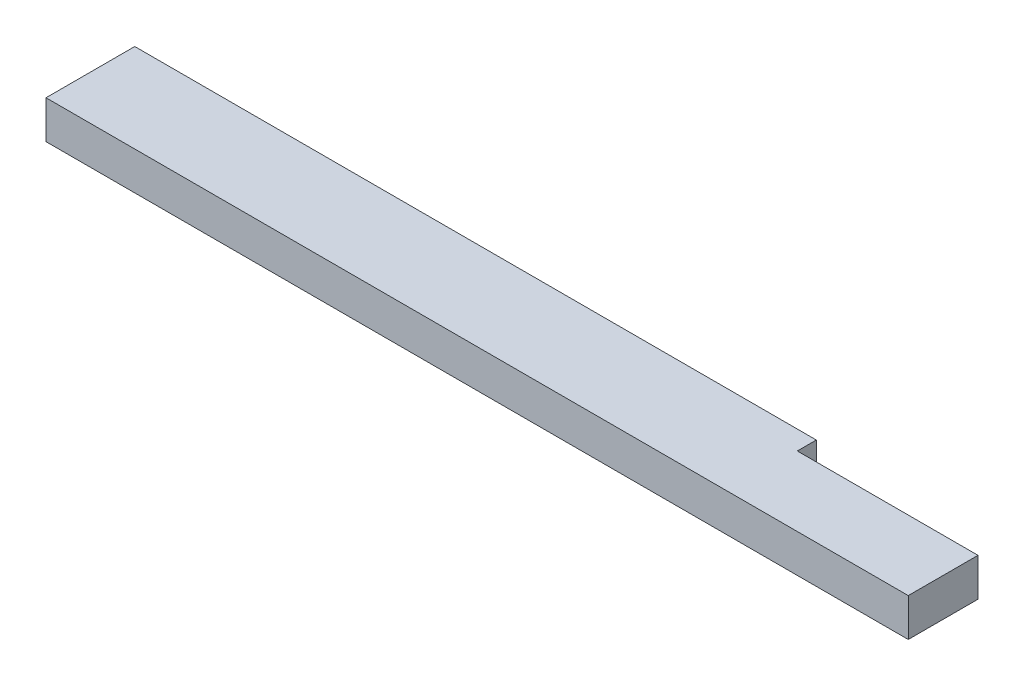
SolidWorks part; units mm, degrees
material "Pine"
ref_plane "Front Plane" through (0, 0, 0) normal (0, 0, 1) x (1, 0, 0)
ref_plane "Top Plane" through (0, 0, 0) normal (0, 1, 0) x (1, 0, 0)
ref_plane "Right Plane" through (0, 0, 0) normal (1, 0, 0) x (0, 0, -1)
sketch "Sketch1" plane through (0, 0, 0) normal (0, 1, 0) x (1, 0, 0)
  line L1 (0, 0) -> (863.6, 0)
  line L2 (0, 0) -> (0, 88.9)
  line L3 (0, 88.9) -> (863.6, 88.9)
  line L4 (863.6, 0) -> (863.6, 88.9)
  dimension "D1" = 88.9
  dimension "D2" = 863.6
extrude "Boss-Extrude1" add sketch "Sketch1" along normal blind 38.1
sketch "Sketch3" plane through (0, 38.1, 0) normal (0, 1, 0) x (1, 0, 0)
  line L5 (863.6, 88.9) -> (682.625, 88.9)
  line L6 (863.6, 88.9) -> (863.6, 69.85)
  line L7 (863.6, 69.85) -> (682.625, 69.85)
  line L8 (682.625, 88.9) -> (682.625, 69.85)
  dimension "D2" = 180.975
  dimension "D4" = 19.05
extrude "Cut-Extrude1" cut sketch "Sketch3" against normal through all
